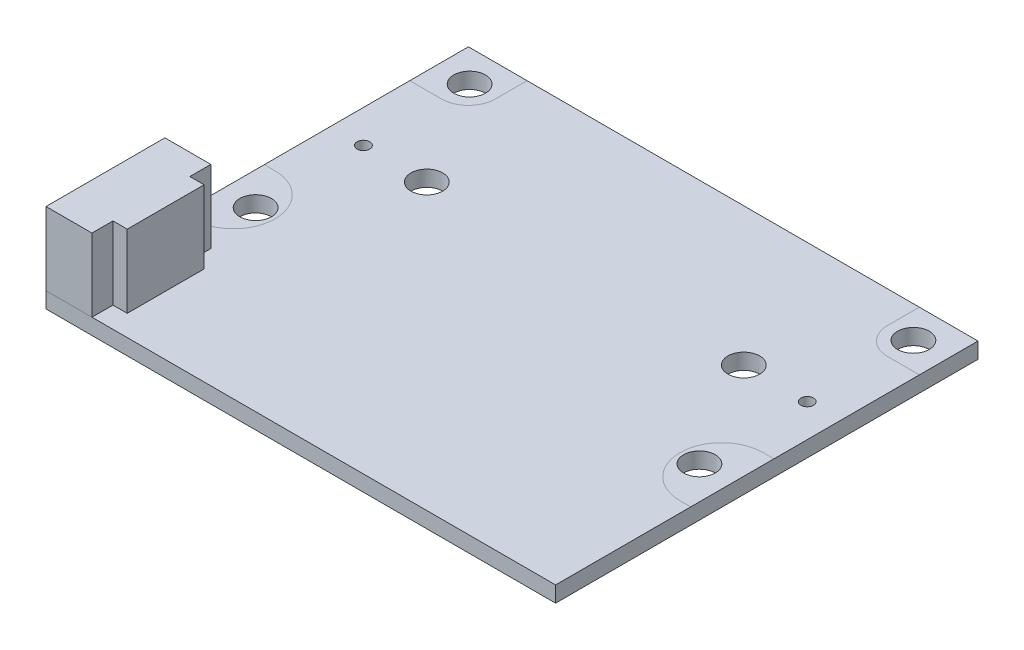
SolidWorks part; units mm, degrees
ref_plane "Front" through (0, 0, 0) normal (0, 0, 1) x (1, 0, 0)
ref_plane "Top" through (0, 0, 0) normal (0, 1, 0) x (1, 0, 0)
ref_plane "Right" through (0, 0, 0) normal (1, 0, 0) x (0, 0, -1)
sketch "Sketch1" plane through (0, 0, 0) normal (0, 1, 0) x (1, 0, 0)
  line L0 (0, 0) -> (0, 16268.1919) construction
  line L1 (0, 0) -> (16268.1919, 0) construction
  line L3 (-16.075, -17.95) -> (16.075, -17.95)
  line L4 (-16.075, -17.95) -> (-16.075, 8.7)
  line L5 (-16.075, 8.7) -> (16.075, 8.7)
  line L6 (16.075, -17.95) -> (16.075, 8.7)
  circle A0 centre (14, 6.7) radius 1
  circle A1 centre (14, -6.8) radius 1
  circle A2 centre (14, 0) radius 0.4
  circle A3 centre (10, 0) radius 1
  circle A4 centre (-14, 0) radius 0.4
  circle A5 centre (-14, -6.8) radius 1
  circle A6 centre (-14, 6.7) radius 1
  circle A7 centre (-10, 0) radius 1
  dimension "D4" = 0.8
  dimension "D5" = 2
  dimension "D6" = 13.5
  dimension "D7" = 28
  dimension "D8" = 2
  dimension "D9" = 2
  dimension "D10" = 20
  dimension "D1" = 26.65
  dimension "D2" = 32.15
  dimension "D3" = 8.7
extrude "Boss-Extrude1" add sketch "Sketch1" along normal blind 1
sketch "Sketch4" plane through (0, 1, 0) normal (0, 1, 0) x (1, 0, 0)
  line L0 (16.075, 5) -> (14.075, 5)
  line L1 (16.075, 8.7) -> (-16.075, 8.7) construction
  line L2 (16.075, -17.95) -> (16.075, 8.7) construction
  line L3 (16.075, 5) -> (16.075, 8.7)
  line L4 (16.075, 8.7) -> (12.375, 8.7)
  line L5 (16.075, -9.425) -> (16.075, -4.175)
  line L6 (0, -0.1285) -> (0, -50000.1285) construction
  line L7 (14, -6.8) -> (-49986, -6.8) construction
  line L8 (14, 6.7) -> (-49986, 6.7) construction
  line L9 (12.375, 8.7) -> (12.375, 6.7)
  line L10 (16.075, -4.175) -> (15.4, -4.175)
  line L11 (16.075, -9.425) -> (15.4, -9.425)
  line L12 (-16.075, -9.425) -> (-15.4, -9.425)
  line L13 (-16.075, -4.175) -> (-15.4, -4.175)
  line L14 (-12.375, 8.7) -> (-12.375, 6.7)
  line L15 (-16.075, -9.425) -> (-16.075, -4.175)
  line L16 (-16.075, 8.7) -> (-12.375, 8.7)
  line L17 (-16.075, 5) -> (-16.075, 8.7)
  line L18 (-16.075, 5) -> (-14.075, 5)
  arc A2 (12.375, 6.7) -> (14.075, 5) centre (14.075, 6.7) ccw
  arc A3 (15.4, -4.175) -> (15.4, -9.425) centre (15.4, -6.8) ccw
  arc A4 (-15.4, -4.175) -> (-15.4, -9.425) centre (-15.4, -6.8) cw
  arc A5 (-12.375, 6.7) -> (-14.075, 5) centre (-14.075, 6.7) cw
  dimension "D1" = 5.25
  dimension "D3" = 3.3
  dimension "D2" = 3.7
split line "Split Line1"
sketch "Sketch5" plane through (0, 1, 0) normal (0, 1, 0) x (1, 0, 0)
  line L0 (-16.075, -14.2) -> (49983.925, -14.2) construction
  line L1 (-16.075, -17.95) -> (-13.175, -17.95)
  line L2 (-16.075, -17.95) -> (-16.075, -10.45)
  line L3 (-16.075, -10.45) -> (-13.175, -10.45)
  line L4 (-13.175, -17.95) -> (-13.175, -16.625)
  line L5 (-13.175, -16.625) -> (-12.275, -16.625)
  line L7 (-13.175, -11.775) -> (-12.275, -11.775)
  line L8 (-12.275, -16.625) -> (-12.275, -11.775)
  line L9 (-13.175, -11.775) -> (-13.175, -10.45)
  point P11 (-16.075, -14.2)
  dimension "D1" = 7.5
  dimension "D2" = 3.8
  dimension "D3" = 2.9
  dimension "D4" = 4.85
extrude "Boss-Extrude3" add sketch "Sketch5" along normal blind 4.6 separate body
ref_point "Point1"
